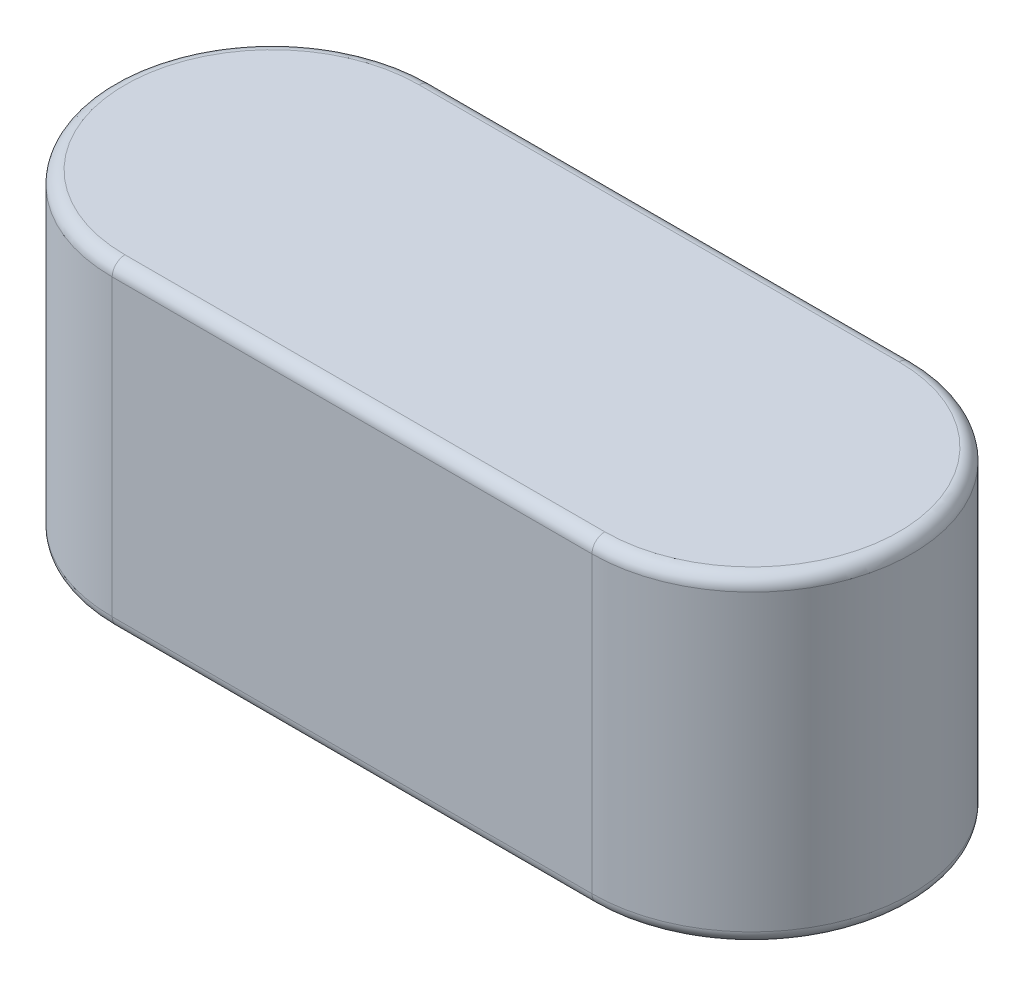
SolidWorks part; units mm, degrees
ref_plane "Front Plane" through (0, 0, 0) normal (0, 0, 1) x (1, 0, 0)
ref_plane "Top Plane" through (0, 0, 0) normal (0, 1, 0) x (1, 0, 0)
ref_plane "Right Plane" through (0, 0, 0) normal (1, 0, 0) x (0, 0, -1)
sketch "Sketch1" plane through (0, 0, 0) normal (0, 1, 0) x (1, 0, 0)
  line L1 (-6, 2) -> (0, 2)
  line L3 (-6, -2) -> (0, -2)
  arc A0 (0, -2) -> (0, 2) centre (0, 0) ccw
  arc A1 (-6, 2) -> (-6, -2) centre (-6, 0) ccw
  dimension "l" = 10
  dimension "b" = 4
extrude "Extrude1" add sketch "Sketch1" along normal blind 4
fillet "Fillet1" radius 0.16 8 edges at (-3, 0, -2) (2, 0, 0) (-8, 0, 0) (-3, 0, 2) (2, 4, 0) (-3, 4, 2) (-3, 4, -2) (-8, 4, 0)
